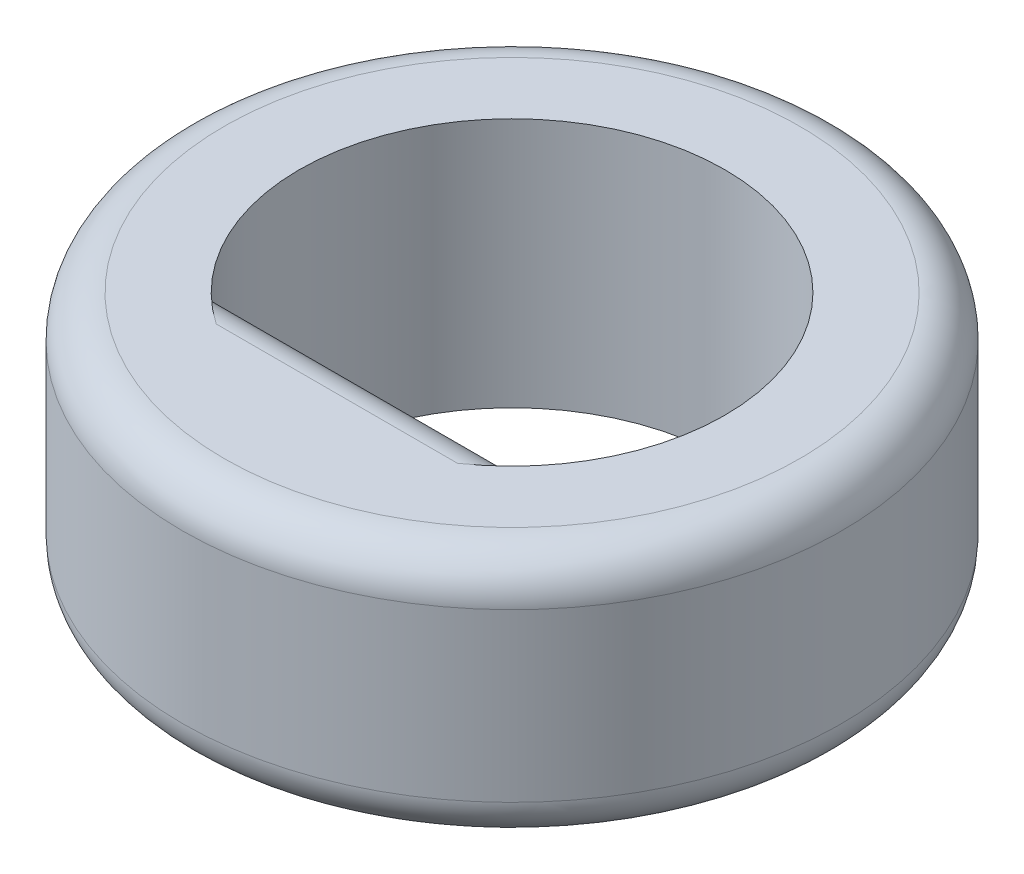
SolidWorks part; units mm, degrees
ref_plane "前视基准面" through (0, 0, 0) normal (0, 0, 1) x (1, 0, 0)
ref_plane "上视基准面" through (0, 0, 0) normal (0, 1, 0) x (1, 0, 0)
ref_plane "右视基准面" through (0, 0, 0) normal (1, 0, 0) x (0, 0, -1)
other "Configuration Table"
sketch "Sketch1" plane through (0, 0, 0) normal (0, 1, 0) x (1, 0, 0)
  line L0 (-1.9856, -1.6) -> (1.9856, -1.6)
  arc A0 (1.9856, -1.6) -> (-1.9856, -1.6) centre (0, 0) ccw
  circle A1 centre (0, 0) radius 3.95
  dimension "D1" = 5.1
  dimension "D3" = 7.9
  dimension "D2" = 1.6
extrude "Boss-Extrude1" add sketch "Sketch1" along normal blind 3
fillet "Fillet1" radius 0.5 4 edges at (0, 0, 1.6) (0, 3, 1.6) (0, 0, 3.95) (0, 3, 3.95)
